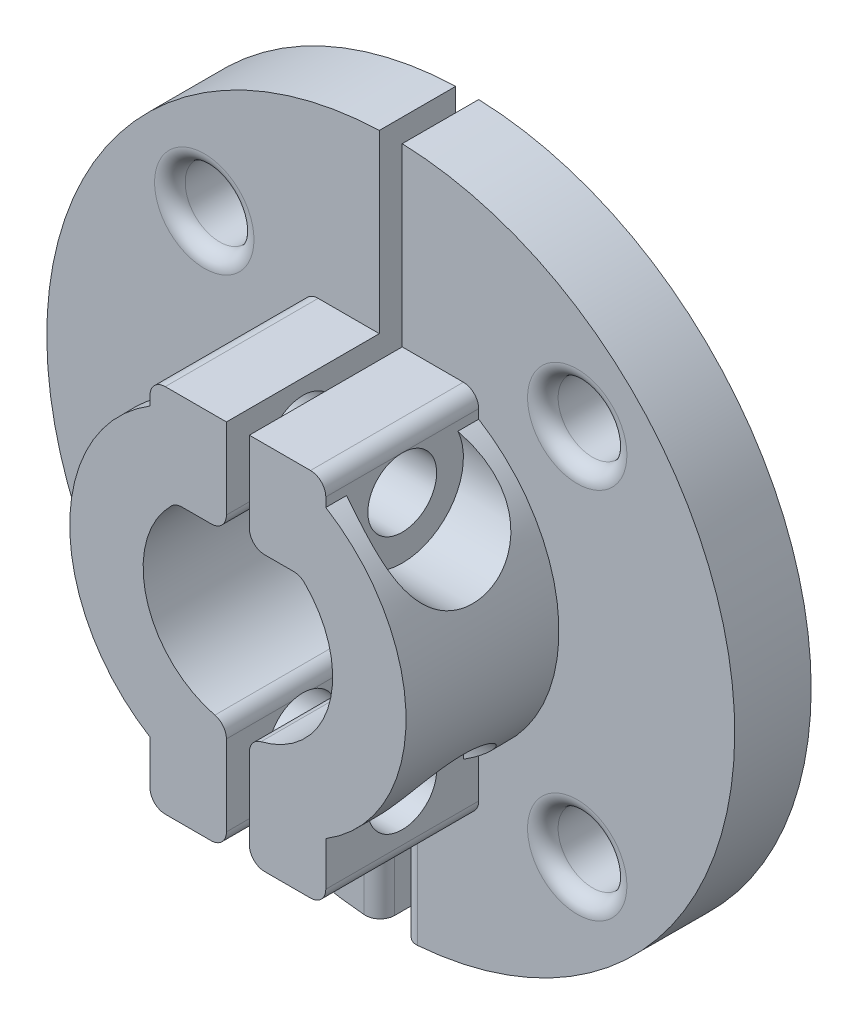
SolidWorks part; units mm, degrees
ref_plane "Front Plane" through (0, 0, 0) normal (0, 0, 1) x (1, 0, 0)
ref_plane "Top Plane" through (0, 0, 0) normal (0, 1, 0) x (1, 0, 0)
ref_plane "Right Plane" through (0, 0, 0) normal (1, 0, 0) x (0, 0, -1)
sketch "Sketch1" plane through (0, 0, 0) normal (0, 0, 1) x (1, 0, 0)
  line L0 (0, 0) -> (0, 22.5) construction
  line L1 (0, 0) -> (22.5, 0) construction
  line L2 (15.9099, 15.9099) -> (0, 0) construction
  circle A7 centre (0, 0) radius 22.5
  circle A8 centre (0, 0) radius 6.2
  circle A10 centre (12.1976, 12.1976) radius 2.25
  circle A11 centre (-12.1976, 12.1976) radius 2.25
  circle A12 centre (12.1976, -12.1976) radius 2.25
  circle A13 centre (-12.1976, -12.1976) radius 2.25
  point P2 (10.6066, 10.6066)
  point P11 (15.9099, 15.9099)
  point P15 (8.8388, 8.8388)
  dimension "D1" = 45
  dimension "D2" = 12.4
  dimension "D3" = 15
  dimension "D7" = 2.5
  dimension "D5" = 4.5
  dimension "D4" = 45
extrude "Boss-Extrude1" add sketch "Sketch1" along normal blind 15
sketch "Sketch2" plane through (0, 0, 15) normal (0, 0, 1) x (1, 0, 0)
  circle A0 centre (0, 0) radius 11
  circle A2 centre (12.1976, 12.1976) radius 2.25 construction
  point P13 (9.9622, 11.9419)
  point P14 (11.7918, 9.9845)
  point P15 (7.8368, 7.7191)
  dimension "D1" = 22
extrude "Cut-Extrude1" cut sketch "Sketch2" against normal blind 10 flip side to cut
sketch "Sketch4" plane through (0, 0, 5) normal (0, 0, 1) x (1, 0, 0)
  line L1 (0.75, -24.0665) -> (-0.75, -24.0665)
  line L2 (0.75, -24.0665) -> (0.75, 24.0665)
  line L3 (0.75, 24.0665) -> (-0.75, 24.0665)
  line L4 (-0.75, -24.0665) -> (-0.75, 24.0665)
  line L5 (0.75, -24.0665) -> (-0.75, 24.0665) construction
  line L6 (0.75, 24.0665) -> (-0.75, -24.0665) construction
  point P0 (0, 0)
  dimension "D1" = 1.5
extrude "Cut-Extrude2" cut sketch "Sketch4" against normal through all both and the other way through all
sketch "Sketch5" plane through (0, 0, 5) normal (0, 0, 1) x (1, 0, 0)
  line L2 (6.325, 8.9997) -> (6.325, 10.9744)
  line L6 (2.6301, 10.9744) -> (2.5636, 10.6971) construction
  line L11 (0.75, 10.9744) -> (6.325, 10.9744)
  line L19 (-0.825, 10.969) -> (-5.75, 9.9718)
  line L20 (-6.325, 8.9997) -> (-5.75, 9.9718)
  arc A8 (6.325, 8.9997) -> (0.75, 10.9744) centre (0, 0) ccw
  arc A9 (-0.825, 10.969) -> (-6.325, 8.9997) centre (0, 0) ccw
  point P0 (0, 0)
  point P10 (0, 4.975)
sketch "Sketch9" plane through (0, 0, 0) normal (0, 0, -1) x (-1, 0, 0)
  line L0 (-4.0435, 4.7) -> (-0.75, 4.7)
  line L1 (-0.75, 6.1545) -> (-0.75, 4.7)
  line L2 (0.75, 6.1545) -> (0.75, 4.7)
  line L3 (0.75, 4.7) -> (4.0435, 4.7)
  arc A0 (-0.75, 6.1545) -> (0.75, 6.1545) centre (0, 0) ccw
  point P3 (0, 6.2)
  arc M6 (0.75, 6.1545) -> (0.75, -6.1545) centre (0, 0) cw
  dimension "D1" = 1.5
extrude "Boss-Extrude7" add sketch "Sketch9" against normal blind 15 contours L1 A0 L0 | L2 L3 M6
sketch "Sketch16" plane through (0, 0, 5) normal (0, 0, 1) x (1, 0, 0)
  line L8 (5.75, 3.475) -> (5.75, 10)
  line L9 (-5.75, 3.475) -> (-5.75, 10.0271)
  line L14 (-5.75, 3.475) -> (-0.75, 10.9744)
  line L15 (0.75, 10.9744) -> (5.75, 3.475)
  line L16 (0, 0) -> (25.9238, 0) construction
  line L25 (0, 0) -> (0, -12.1547) construction
  line L26 (-0.75, -8.2496) -> (-5.75, -8.2496)
  line L27 (-0.75, -8.2496) -> (-0.75, -13.2496)
  line L28 (-0.75, -13.2496) -> (-5.75, -13.2496)
  line L29 (-5.75, -8.2496) -> (-5.75, -13.2496)
  line L30 (0.75, -13.2496) -> (5.75, -13.2496)
  line L31 (5.75, -8.2496) -> (5.75, -13.2496)
  line L32 (0.75, -8.2496) -> (5.75, -8.2496)
  line L33 (0.75, -8.2496) -> (0.75, -13.2496)
  line L34 (-5.75, -8.2496) -> (-0.75, -10.9744)
  line L35 (5.75, -8.2496) -> (0.75, -10.9744)
  line L36 (0.75, 10.9744) -> (5.75, 10.9744)
  line L37 (5.75, 10) -> (5.75, 10.9744)
  line L38 (-0.75, 10.9744) -> (-5.75, 10.9744)
  line L39 (-5.75, 10.0271) -> (-5.75, 10.9744)
  line L44 (0.75, -10.9744) -> (0.75, -6.1545) construction
  circle A0 centre (12.1976, 12.1976) radius 2.25 construction
  circle A1 centre (-12.1976, 12.1976) radius 2.25 construction
  arc A2 (0.75, -10.9744) -> (0.75, 10.9744) centre (0, 0) ccw construction
  point P0 (9.9622, 11.9419)
  point P20 (-9.9622, 11.9419)
  dimension "D1" = 5
  dimension "D3" = 5
  dimension "D4" = 5
extrude "Boss-Extrude9" add sketch "Sketch16" along normal blind 10 contours L9 L39 L38 L14 | L8 L37 L36 L15 | L31 L30 L33 L32 | L29 L28 L27 L26
fillet "Fillet1" radius 1 1 edges at (-4.0435, 4.7, 7.5)
fillet "Fillet2" radius 1 1 edges at (4.0435, 4.7, 7.5)
fillet "Fillet14" radius 1 1 edges at (-0.75, -6.1545, 7.5)
fillet "Fillet19" radius 1 1 edges at (-0.75, -13.2496, 10)
fillet "Fillet20" radius 1 1 edges at (0.75, -13.2496, 10)
fillet "Fillet21" radius 1 1 edges at (-0.75, -17.3686, 5)
fillet "Fillet22" radius 1 1 edges at (0.75, -17.3686, 5)
fillet "Fillet25" radius 1 2 edges at (-9.9476, 12.1976, 5) (-14.4476, 12.1976, 0)
fillet "Fillet26" radius 1 2 edges at (14.4476, 12.1976, 5) (14.4476, 12.1976, 0)
fillet "Fillet27" radius 1 2 edges at (9.9476, -12.1976, 0) (14.4476, -12.1976, 5)
fillet "Fillet33" radius 1 2 edges at (-9.9476, -12.1976, 5) (-9.9476, -12.1976, 0)
fillet "Fillet35" radius 1 1 edges at (0.75, -6.1545, 7.5)
fillet "Fillet36" radius 1 1 edges at (-0.75, 4.7, 7.5)
fillet "Fillet37" radius 1 1 edges at (0.75, 4.7, 7.5)
sketch "Sketch17" plane through (-5.75, 0, 0) normal (-1, 0, 0) x (0, 0, 1)
  line L0 (10, 10.9744) -> (10, -11.375) construction
  line L1 (15, 10.9744) -> (5, 10.9744) construction
  line L2 (10, 4.475) -> (18.9183, 4.475) construction
  line L3 (10, 4.475) -> (4.8541, 4.475) construction
  line L4 (10, 4.475) -> (10, 10.9744) construction
  line L5 (10, -5.975) -> (10, -11.375) construction
  circle A0 centre (10, 7.7247) radius 2.25
  circle A1 centre (10, -9.125) radius 2.25
  point P4 (10, 4.475)
  point P11 (10, -5.975)
  point P14 (10, -11.375)
  point P19 (10, 5.4747)
  point P20 (10, -6.875)
  point P21 (10, 9.9747)
  dimension "D2" = 5.975
  dimension "D3" = 4.5
  dimension "D4" = 4.5
  dimension "D1" = 4.475
  dimension "D5" = 0.9
extrude "Cut-Extrude3" cut sketch "Sketch17" against normal through all both and the other way through all
sketch "Sketch20" plane through (-5.75, 0, 0) normal (-1, 0, 0) x (0, 0, 1)
  circle A0 centre (10, -9.125) radius 4
  circle A2 centre (10, 7.7247) radius 4
  dimension "D1" = 8
sketch "Sketch21" plane through (5.75, 0, 0) normal (1, 0, 0) x (0, 0, -1)
  circle A0 centre (-10, 7.7247) radius 4
  circle A1 centre (-10, -9.125) radius 4
extrude "Cut-Extrude9" cut sketch "Sketch20" along normal through all
extrude "Cut-Extrude10" cut sketch "Sketch21" along normal through all
fillet "Fillet38" radius 1 2 edges at (-5.75, 10.9744, 10) (-5.75, -13.2496, 10)
fillet "Fillet39" radius 1 2 edges at (5.75, 10.9744, 10) (5.75, -13.2496, 10)
